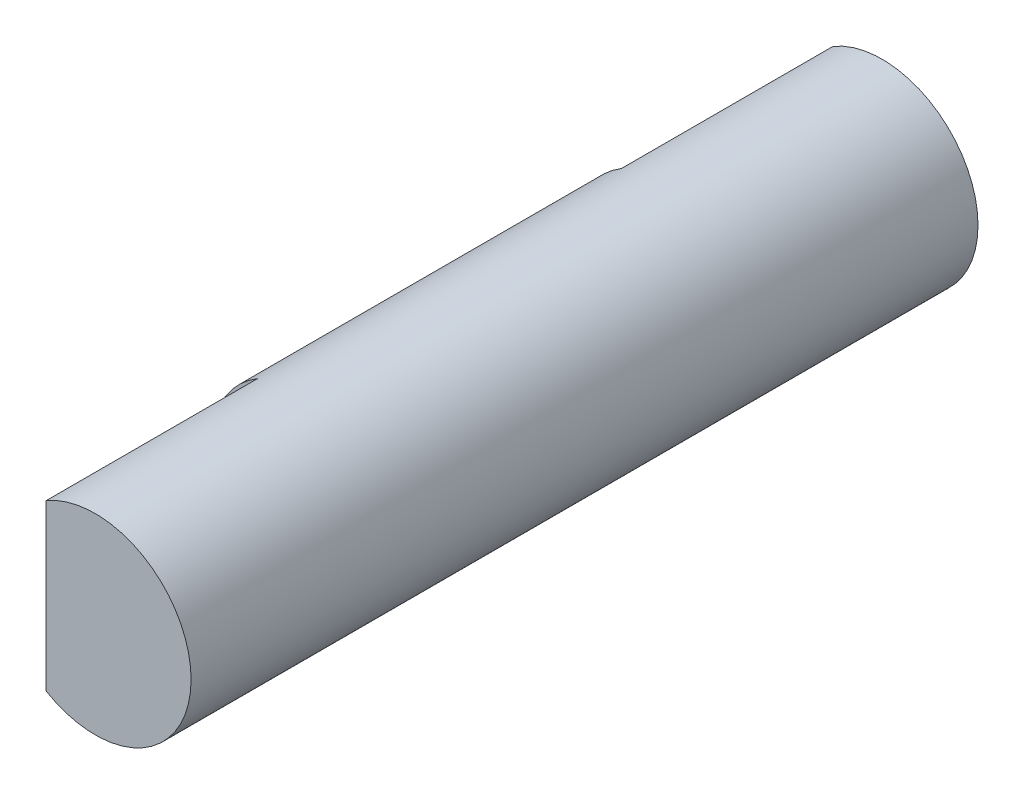
SolidWorks part; units mm, degrees
ref_plane "Front Plane" through (0, 0, 0) normal (0, 0, 1) x (1, 0, 0)
ref_plane "Top Plane" through (0, 0, 0) normal (0, 1, 0) x (1, 0, 0)
ref_plane "Right Plane" through (0, 0, 0) normal (1, 0, 0) x (0, 0, -1)
sketch "Sketch2" plane through (0, 0, 0) normal (0, 0, 1) x (1, 0, 0)
  circle A0 centre (0, 0) radius 1.95
  dimension "D1" = 3.9
extrude "Boss-Extrude1" add sketch "Sketch2" along normal mid plane 16
sketch "Sketch4" plane through (0, 0, -8) normal (0, 0, -1) x (-1, 0, 0)
  line L0 (1, 1.6741) -> (1, -1.6741)
  arc A0 (1, -1.6741) -> (1, 1.6741) centre (0, 0) ccw
  dimension "D2" = 3.9
  dimension "D1" = 1
extrude "Cut-Extrude1" cut sketch "Sketch4" against normal blind 4.3
mirror "Mirror1" about plane through (0, 0, 0) normal (0, 0, 1) of "Cut-Extrude1"
